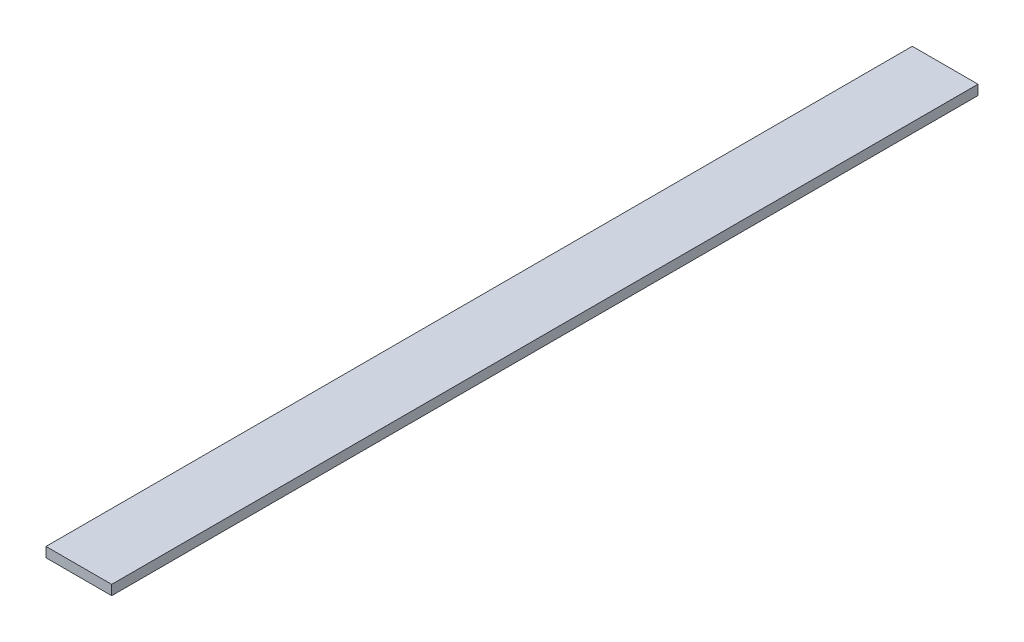
SolidWorks part; units mm, degrees
material "Balsa"
ref_plane "Front Plane" through (0, 0, 0) normal (0, 0, 1) x (1, 0, 0)
ref_plane "Top Plane" through (0, 0, 0) normal (0, 1, 0) x (1, 0, 0)
ref_plane "Right Plane" through (0, 0, 0) normal (1, 0, 0) x (0, 0, -1)
sketch "Sketch1" plane through (0, 0, 0) normal (0, 1, 0) x (1, 0, 0)
  line L1 (-36.5161, 316.7563) -> (-6.5161, 316.7563)
  line L2 (-36.5161, 316.7563) -> (-36.5161, -87.2437)
  line L3 (-36.5161, -87.2437) -> (-6.5161, -87.2437)
  line L4 (-6.5161, 316.7563) -> (-6.5161, -87.2437)
  line L5 (-36.5161, 316.7563) -> (-6.5161, -87.2437) construction
  line L6 (-36.5161, -87.2437) -> (-6.5161, 316.7563) construction
  point P0 (-21.5161, 114.7563)
  dimension "D1" = 404
  dimension "D2" = 30
extrude "Boss-Extrude1" add sketch "Sketch1" along normal blind 4.5
sketch "Sketch2" plane through (-6.5161, 0, 0) normal (1, 0, 0) x (0, 0, -1)
  line L0 (-87.2437, 4.5) -> (-78.8737, 4.5)
  line L1 (-87.2437, 4.5) -> (-87.2437, 0)
  line L2 (-78.8737, 4.5) -> (-78.8737, 0)
  line L3 (-87.2437, 0) -> (-78.8737, 0)
  line L4 (-87.2437, 4.5) -> (316.7563, 4.5) construction
  line L5 (-87.2437, 0) -> (316.7563, 0) construction
  dimension "D1" = 8.37
  dimension "D2" = 4.5
extrude "Cut-Extrude1" cut sketch "Sketch2" against normal blind 40
